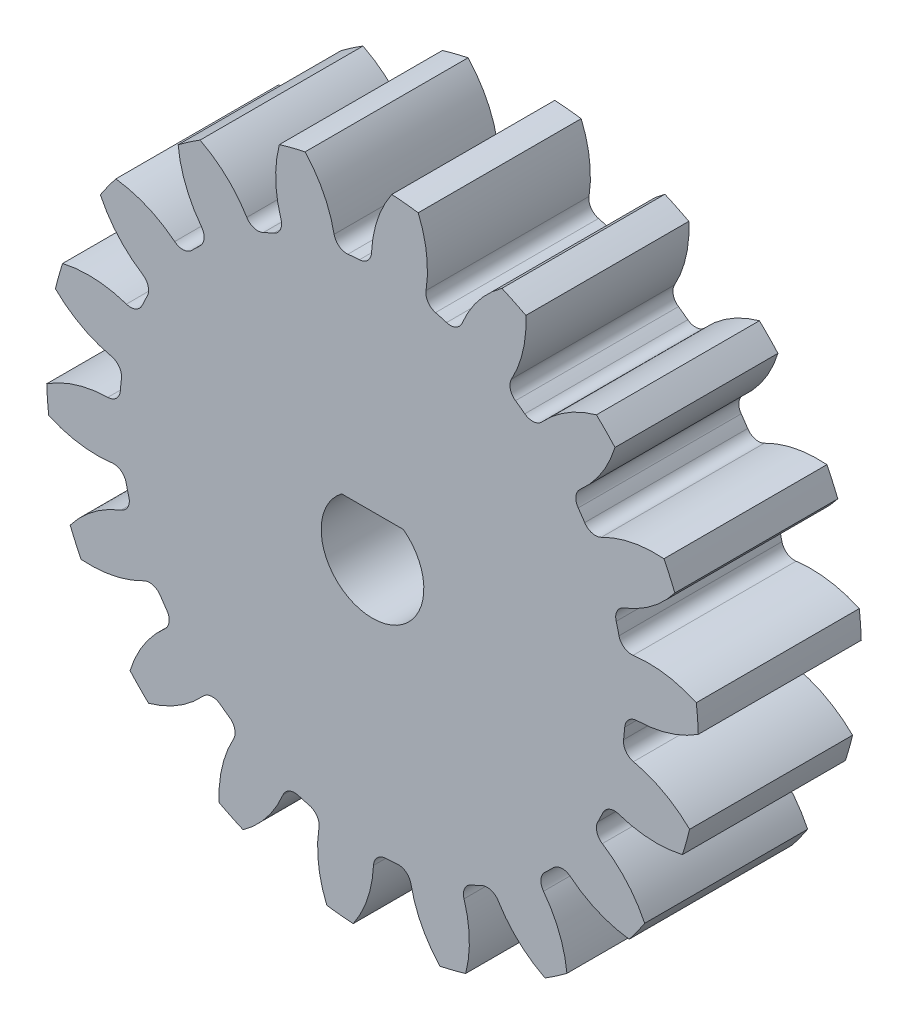
SolidWorks part; units mm, degrees
ref_plane "Front" through (0, 0, 0) normal (0, 0, 1) x (1, 0, 0)
ref_plane "Top" through (0, 0, 0) normal (0, 1, 0) x (1, 0, 0)
ref_plane "Right" through (0, 0, 0) normal (1, 0, 0) x (0, 0, -1)
sketch "Sketch3" plane through (0, 0, 0) normal (0, 0, 1) x (1, 0, 0)
  circle A0 centre (0, 0) radius 12.7
  dimension "od" = 25.4
extrude "gearBody" add sketch "Sketch3" along normal blind 6.35
sketch "Sketch2" plane through (0, 0, 0) normal (0, 0, 1) x (1, 0, 0)
  line L0 (0, 0) -> (10.2236, 4.2347) construction
  line L1 (13.3591, -4.4187) -> (0, 0) construction
  line L2 (0, 0) -> (36.3143, 0) construction
  line L3 (11.4292, -0.1374) -> (11.2291, -2.1338) construction
  line L5 (11.3291, -1.1356) -> (0, 0) construction
  line L7 (0, 0) -> (11.0659, 0) construction
  arc A0 (11.0637, -0.2221) -> (10.8877, -1.9783) centre (0, 0) ccw construction
  arc A1 (12.6927, 0.4305) -> (12.3547, -2.9412) centre (0, 0) ccw construction
  arc A2 (11.4292, -0.1374) -> (11.2291, -2.1338) centre (0, 0) ccw construction
  arc A3 (9.7812, -1.2052) -> (9.8258, -0.7602) centre (0, 0) ccw
  arc A4 (13.3591, -4.4187) -> (10.1678, -1.7534) centre (9.1796, -6.1797) ccw
  arc A5 (13.3591, -4.4187) -> (13.9704, 1.6792) centre (0, 0) ccw
  arc A6 (13.9704, 1.6792) -> (10.3136, -0.2997) centre (10.2236, 4.2347) cw
  arc A7 (9.8258, -0.7602) -> (10.3136, -0.2997) centre (10.3235, -0.7987) cw
  arc A8 (10.1678, -1.7534) -> (9.7812, -1.2052) centre (10.2766, -1.2662) cw
  point P6 (13.9704, 1.6792)
  point P22 (13.3591, -4.4187)
  dimension "baseDia" = 22.1319
  dimension "od" = 25.4
  dimension "pd" = 22.86
  dimension "rd" = 19.7104
  dimension "rFillet" = 0.4991
  dimension "pointX" = 13.9704
  dimension "pointY" = 1.6792
  dimension "CTT" = 1.9964
  dimension "flankCenterAngle" = 22.5
extrude "toothCut" cut sketch "Sketch2" along normal through all
pattern_circular "CirPattern1" count 18 over 360 about axis through (0, 0, 0) along (0, 0, 1) of "toothCut"
sketch "hub1Dia" plane through (0, 0, 0) normal (0, 0, -1) x (-1, 0, 0)
  circle A0 centre (0, 0) radius 25.4
  dimension "hub1Dia" = 50.8
extrude "hub1" [suppressed] add sketch "hub1Dia" along normal blind 19.05
sketch "hub2Dia" plane through (0, 0, 6.35) normal (0, 0, 1) x (1, 0, 0)
  circle A0 centre (0, 0) radius 21.844
  dimension "hub2dia" = 43.688
extrude "hub2" [suppressed] add sketch "hub2Dia" along normal blind 16.002
sketch "boreDia" plane through (0, 0, 0) normal (0, 0, 1) x (1, 0, 0)
  line L0 (-1.2, 1.6) -> (1.2, 1.6)
  arc A0 (-1.2, 1.6) -> (1.2, 1.6) centre (0, 0) ccw
  point P5 (0.2675, 1.7817)
  dimension "D1" = 2.4
  dimension "boreDia" = 4
extrude "bore" cut sketch "boreDia" against normal mid plane 25.4
chamfer "hub2Chamfer" [suppressed] distance 0.508 angle 45
chamfer "hub2BoreChamfer" [suppressed] distance 0.508 angle 45
chamfer "hub1BoreChamfer" [suppressed] distance 0.508 angle 45
chamfer "hub1Chamfer" [suppressed] distance 0.508 angle 45
chamfer "BoreChamfer2" [suppressed] distance 0.508 angle 45
chamfer "boreChamfer1" [suppressed] distance 0.508 angle 45
